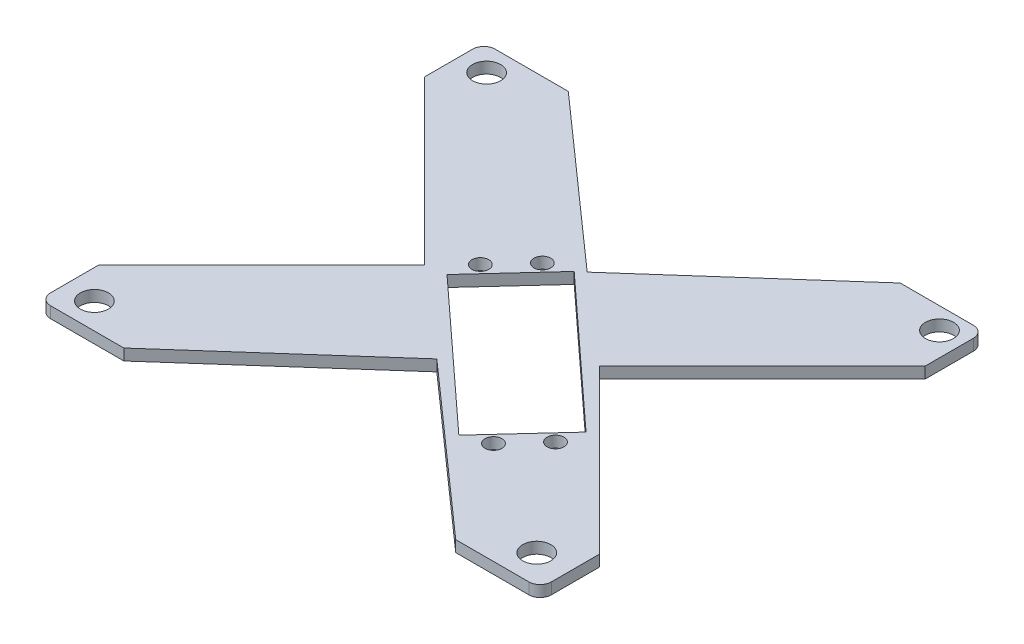
SolidWorks part; units mm, degrees
ref_plane "Front Plane" through (0, 0, 0) normal (0, 0, 1) x (1, 0, 0)
ref_plane "Top Plane" through (0, 0, 0) normal (0, 1, 0) x (1, 0, 0)
ref_plane "Right Plane" through (0, 0, 0) normal (1, 0, 0) x (0, 0, -1)
sketch "Sketch2" plane through (0, 0, 0) normal (0, 1, 0) x (1, 0, 0)
  line L1 (-56.515, 50.165) -> (56.515, 50.165)
  line L2 (-56.515, 50.165) -> (-56.515, -50.165)
  line L3 (-56.515, -50.165) -> (56.515, -50.165)
  line L4 (56.515, 50.165) -> (56.515, -50.165)
  line L5 (-56.515, 50.165) -> (56.515, -50.165) construction
  line L6 (-56.515, -50.165) -> (56.515, 50.165) construction
  point P0 (0, 0)
  dimension "D1" = 113.03
  dimension "D2" = 100.33
extrude "Boss-Extrude1" add sketch "Sketch2" along normal blind 2.54
fillet "Fillet1" radius 2.54 1 edges at (-56.515, 1.27, -50.165)
fillet "Fillet2" radius 2.54 3 edges at (56.515, 1.27, -50.165) (56.515, 1.27, 50.165) (-56.515, 1.27, 50.165)
sketch "Sketch4" plane through (0, 2.54, 0) normal (0, 1, 0) x (1, 0, 0)
  line L0 (55.7711, 49.4211) -> (-55.7711, -49.4211) construction
  line L1 (-55.7711, 49.4211) -> (55.7711, -49.4211) construction
  line L2 (-37.4614, 50.165) -> (0, 16.9689)
  line L3 (53.975, 50.165) -> (-53.975, 50.165) construction
  line L4 (0, 16.9689) -> (37.4614, 50.165)
  line L5 (37.4614, 50.165) -> (-37.4614, 50.165)
  line L6 (-56.515, 0) -> (56.515, 0) construction
  line L7 (-56.515, 47.625) -> (-56.515, -47.625) construction
  line L8 (56.515, -47.625) -> (56.515, 47.625) construction
  line L9 (0, -16.9689) -> (37.4614, -50.165)
  line L10 (-37.4614, -50.165) -> (0, -16.9689)
  line L11 (37.4614, -50.165) -> (-37.4614, -50.165)
  line L12 (-56.515, 36.7211) -> (-19.783, -0.0109)
  line L13 (-19.783, -0.0109) -> (-56.515, -36.7429)
  line L14 (-56.515, -36.7429) -> (-56.515, 36.7211)
  line L15 (0, 50.165) -> (0, -50.165) construction
  line L16 (19.783, -0.0109) -> (56.515, -36.7429)
  line L17 (56.515, 36.7211) -> (19.783, -0.0109)
  line L18 (56.515, -36.7429) -> (56.515, 36.7211)
  arc A0 (56.515, 47.625) -> (53.975, 50.165) centre (53.975, 47.625) ccw construction
  arc A1 (-56.515, -47.625) -> (-53.975, -50.165) centre (-53.975, -47.625) ccw construction
  arc A2 (-53.975, 50.165) -> (-56.515, 47.625) centre (-53.975, 47.625) ccw construction
  arc A3 (53.975, -50.165) -> (56.515, -47.625) centre (53.975, -47.625) ccw construction
  dimension "D1" = 12.7
  dimension "D2" = 12.7
  dimension "D3" = 12.7
  dimension "D4" = 12.7
extrude "Cut-Extrude1" cut sketch "Sketch4" against normal through all
sketch "Sketch5" plane through (0, 2.54, 0) normal (0, 1, 0) x (1, 0, 0)
  line L0 (-55.7711, 49.4211) -> (55.7711, -49.4211) construction
  line L1 (-55.7711, -49.4211) -> (55.7711, 49.4211) construction
  arc A0 (-53.975, 50.165) -> (-56.515, 47.625) centre (-53.975, 47.625) ccw construction
  arc A1 (53.975, -50.165) -> (56.515, -47.625) centre (53.975, -47.625) ccw construction
  arc A2 (-56.515, -47.625) -> (-53.975, -50.165) centre (-53.975, -47.625) ccw construction
  arc A3 (56.515, 47.625) -> (53.975, 50.165) centre (53.975, 47.625) ccw construction
  circle A4 centre (-50.3458, 44.6135) radius 3.175
  circle A5 centre (49.1656, -43.5676) radius 3.175
  circle A6 centre (51.157, 45.3324) radius 3.175
  circle A7 centre (-49.9768, -44.2865) radius 3.175
  point P24 (0, 0)
  point P25 (0, 0)
  point P26 (0, 0)
  point P27 (0, 0)
  dimension "D1" = 6.35
  dimension "D5" = 6.35
  dimension "D2" = 135.128
  dimension "D4" = 88.9
  dimension "D6" = 88.9
extrude "Cut-Extrude2" cut sketch "Sketch5" against normal through all
sketch "Sketch8" plane through (0, 2.54, 0) normal (0, 1, 0) x (1, 0, 0)
  line L0 (-15.343, 0.6717) -> (17.3957, -29.3945)
  line L1 (17.3957, -29.3945) -> (31.1403, -14.4282)
  line L2 (31.1403, -14.4282) -> (-1.5985, 15.638)
  line L3 (-1.5985, 15.638) -> (-15.343, 0.6717)
  dimension "D1" = 20.32
  dimension "D2" = 44.45
extrude "Cut-Extrude3" cut sketch "Sketch8" against normal through all
sketch "Sketch9" plane through (0, 2.54, 0) normal (0, 1, 0) x (1, 0, 0)
  line L0 (17.3957, -29.3945) -> (31.1403, -14.4282) construction
  line L1 (37.4614, -50.165) -> (0, -16.9689) construction
  line L2 (14.7709, 0.6049) -> (1.0264, -14.3614) construction
  line L3 (31.1403, -14.4282) -> (-1.5985, 15.638) construction
  line L4 (-15.343, 0.6717) -> (17.3957, -29.3945) construction
  circle A0 centre (22.9384, -27.1143) radius 1.905
  circle A1 centre (29.6327, -19.8125) radius 1.905
  circle A2 centre (-13.5419, 6.3881) radius 1.905
  circle A3 centre (-6.8352, 13.6785) radius 1.905
  dimension "D1" = 3.81
  dimension "D2" = 2.54
  dimension "D4" = 9.906
  dimension "D5" = 3.81
  dimension "D3" = 7.62
extrude "Cut-Extrude4" cut sketch "Sketch9" against normal blind 5.08
sketch "Sketch10" plane through (0, 2.54, 0) normal (0, 1, 0) x (1, 0, 0)
